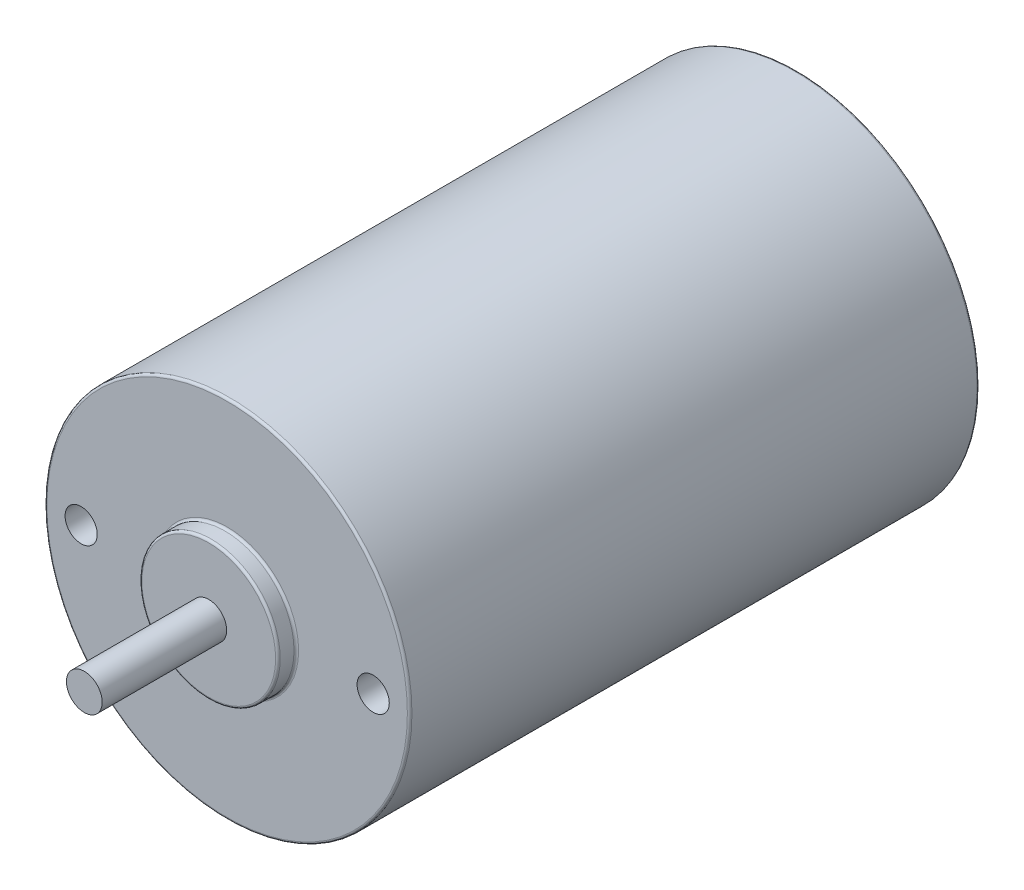
SolidWorks part; units mm, degrees
material "Gray Cast Iron"
ref_plane "Front Plane" through (0, 0, 0) normal (0, 0, 1) x (1, 0, 0)
ref_plane "Top Plane" through (0, 0, 0) normal (0, 1, 0) x (1, 0, 0)
ref_plane "Right Plane" through (0, 0, 0) normal (1, 0, 0) x (0, 0, -1)
sketch "Sketch2" plane through (0, 0, 0) normal (0, 1, 0) x (1, 0, 0)
  line L0 (31.9852, 0) -> (0, 0) construction
  line L1 (0, 0) -> (0, 41.695) construction
  line L2 (1.55, -26.375) -> (1.55, 26.375)
  line L3 (1.55, 26.375) -> (6.015, 26.375)
  line L4 (6.015, 26.375) -> (6.015, 24.775)
  line L5 (6.015, 24.775) -> (15.875, 24.775)
  line L6 (15.875, 24.775) -> (15.875, -24.775)
  line L7 (6.015, -24.775) -> (15.875, -24.775)
  line L8 (6.015, -26.375) -> (6.015, -24.775)
  line L9 (1.55, -26.375) -> (6.015, -26.375)
  point P11 (15.875, 0)
  point P14 (1.55, 0)
  dimension "D1" = 3.1
  dimension "D2" = 31.75
  dimension "D3" = 49.55
  dimension "D4" = 12.03
  dimension "D5" = 52.75
revolve "body" add sketch "Sketch2" angle 360 about L1
sketch "Sketch4" plane through (0, 0, 0) normal (0, 0, 1) x (1, 0, 0)
  circle A0 centre (0, 0) radius 1.555
  dimension "D1" = 3.11
extrude "shaft" add sketch "Sketch4" along normal blind 37.2
fillet "Fillet1" radius 0.2 6 edges at (15.875, 0, -24.775) (6.015, 0, -24.775) (6.015, 0, -26.375) (15.875, 0, 24.775) (6.015, 0, 24.775) (6.015, 0, 26.375)
sketch "Sketch6" plane through (0, 0, 24.775) normal (0, 0, 1) x (1, 0, 0)
  circle A0 centre (-12.7, 0) radius 1.4
  circle A1 centre (12.7, 0) radius 1.4
  dimension "D1" = 2.8
  dimension "D2" = 25.4
  dimension "D3" = 12.7
extrude "#6-32 threaded" cut sketch "Sketch6" against normal blind 5
